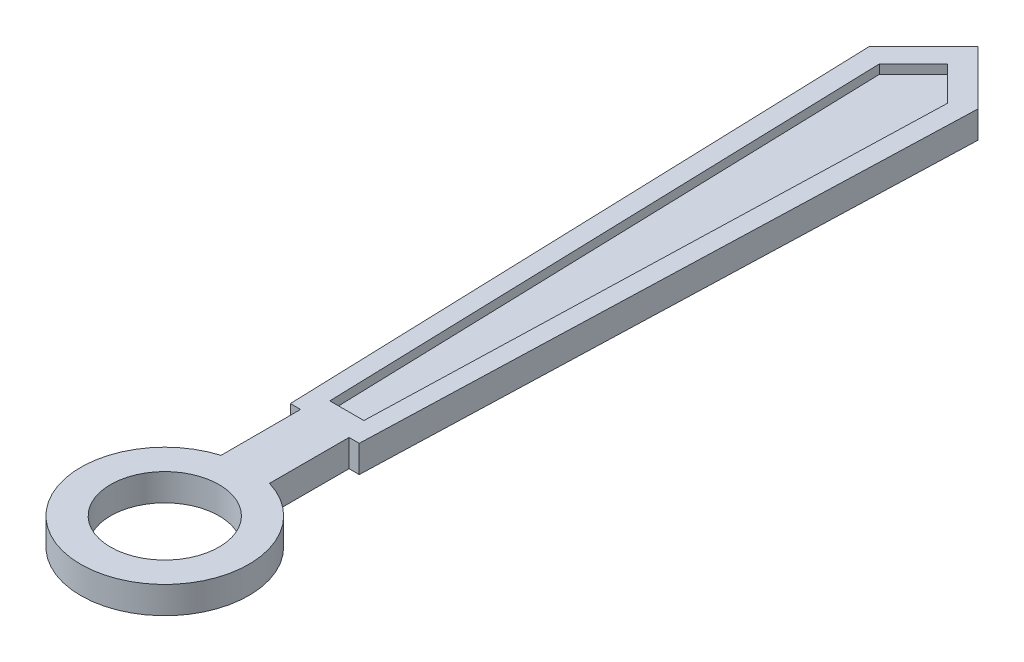
SolidWorks part; units mm, degrees
ref_plane "Front Plane" through (0, 0, 0) normal (0, 0, 1) x (1, 0, 0)
ref_plane "Top Plane" through (0, 0, 0) normal (0, 1, 0) x (1, 0, 0)
ref_plane "Right Plane" through (0, 0, 0) normal (1, 0, 0) x (0, 0, -1)
sketch "Sketch1" plane through (0, 0, 0) normal (0, 1, 0) x (1, 0, 0)
  line L1 (-0.2684, 1.7709) -> (-0.2684, 0.8909)
  line L2 (0.2684, 1.7709) -> (0.2684, 0.8909)
  line L3 (0, 9) -> (0.6, 8.4)
  line L5 (-0.6, 8.4) -> (0, 9)
  line L6 (0.6, 8.4) -> (0.381, 1.7709)
  line L7 (-0.6, 8.4) -> (-0.381, 1.7709)
  line L9 (-0.381, 1.7709) -> (-0.2684, 1.7709)
  line L10 (0.381, 1.7709) -> (0.2684, 1.7709)
  arc A2 (-0.2684, 0.8909) -> (0.2684, 0.8909) centre (0, 0) ccw
extrude "Boss-Extrude1" add sketch "Sketch1" along normal blind 0.3
sketch "Sketch2" plane through (0, 0, 0) normal (0, 1, 0) x (1, 0, 0)
  circle A0 centre (0, 0) radius 0.6
extrude "Cut-Extrude2" cut sketch "Sketch2" along normal blind 0.3
sketch "Sketch4" plane through (0, 0.3, 0) normal (0, 1, 0) x (1, 0, 0)
  line L0 (0, 8.6626) -> (0.3772, 8.2854)
  line L1 (0.3772, 8.2854) -> (0.1886, 2.0149)
  line L2 (0.1886, 2.0149) -> (-0.1886, 2.0149)
  line L4 (-0.3772, 8.2854) -> (-0.1886, 2.0149)
  line L5 (0, 8.6626) -> (-0.3772, 8.2854)
  point P7 (0, 2.0149)
extrude "Cut-Extrude3" cut sketch "Sketch4" against normal blind 0.1
